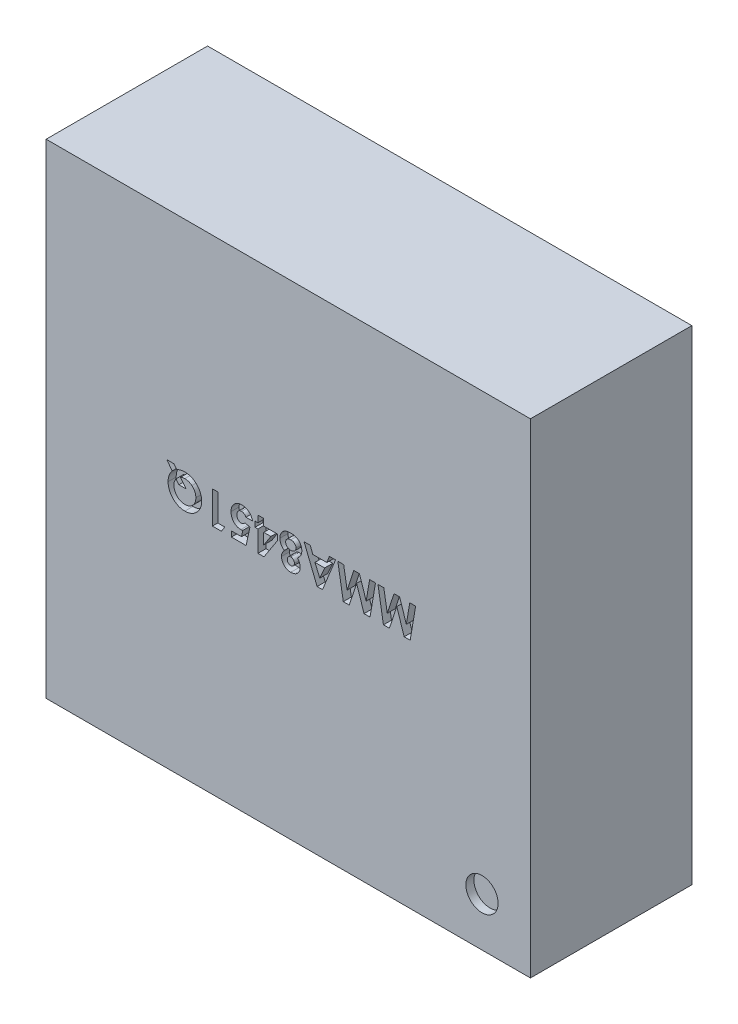
SolidWorks part; units mm, degrees
ref_plane "Piano frontale" through (0, 0, 0) normal (0, 0, 1) x (1, 0, 0)
ref_plane "Piano superiore" through (0, 0, 0) normal (0, 1, 0) x (1, 0, 0)
ref_plane "Piano destro" through (0, 0, 0) normal (1, 0, 0) x (0, 0, -1)
sketch "Schizzo1" plane through (0, 0, 0) normal (0, 0, 1) x (1, 0, 0)
  line L1 (0, 0) -> (3, 0)
  line L2 (0, 0) -> (0, 3)
  line L3 (0, 3) -> (3, 3)
  line L4 (3, 0) -> (3, 3)
  dimension "D1" = 3
  dimension "D2" = 3
extrude "Estrusione-Estrusione1" add sketch "Schizzo1" along normal blind 1
sketch "Schizzo2" plane through (0, 0, 1) normal (0, 0, 1) x (1, 0, 0)
  line L0 (2.294, 1.6394) -> (0.605, 1.6394) construction
  text T0 "<b>MMA8451Q</b>" font "Century Gothic" height 0.2
extrude "Taglio-Estrusione1" cut sketch "Schizzo2" against normal blind 0.05
sketch "Schizzo3" plane through (0, 0, 1) normal (0, 0, 1) x (1, 0, 0)
  line L0 (0, 0) -> (3, 0) construction
  line L1 (3, 0) -> (3, 3) construction
  circle A0 centre (2.7, 0.3) radius 0.1
  dimension "D1" = 0.3
  dimension "D2" = 0.3
extrude "Taglio-Estrusione2" cut sketch "Schizzo3" against normal blind 0.05
